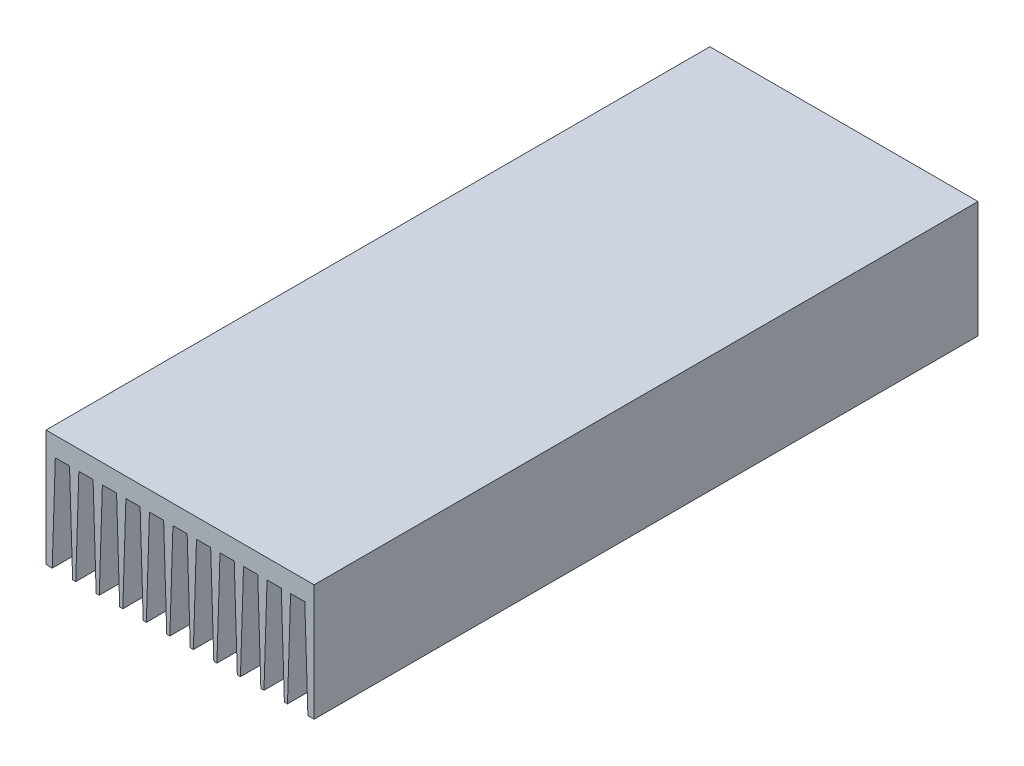
SolidWorks part; units mm, degrees
ref_plane "Plano frontal" through (0, 0, 0) normal (0, 0, 1) x (1, 0, 0)
ref_plane "Plano superior" through (0, 0, 0) normal (0, 1, 0) x (1, 0, 0)
ref_plane "Plano direito" through (0, 0, 0) normal (1, 0, 0) x (0, 0, -1)
sketch "Esboço1" plane through (0, 0, 0) normal (0, 0, 1) x (1, 0, 0)
  line L0 (0.117, 0.0008) -> (0.117, 50.0008)
  line L1 (0.117, 50.0008) -> (115.217, 50.0008)
  line L2 (115.217, 50.0008) -> (115.217, 0.0008)
  line L3 (0.117, 0.0008) -> (115.217, 0.0008) construction
  line L4 (0.117, 41.7008) -> (4.117, 41.7008) construction
  line L5 (4.117, 41.7008) -> (10.217, 41.7008)
  line L6 (10.217, 41.7008) -> (14.217, 41.7008) construction
  line L7 (14.217, 41.7008) -> (20.317, 41.7008)
  line L8 (20.317, 41.7008) -> (24.317, 41.7008) construction
  line L9 (24.317, 41.7008) -> (30.417, 41.7008)
  line L10 (30.417, 41.7008) -> (34.417, 41.7008) construction
  line L11 (34.417, 41.7008) -> (40.517, 41.7008)
  line L12 (40.517, 41.7008) -> (44.517, 41.7008) construction
  line L13 (44.517, 41.7008) -> (50.617, 41.7008)
  line L14 (50.617, 41.7008) -> (54.617, 41.7008) construction
  line L15 (54.617, 41.7008) -> (60.717, 41.7008)
  line L16 (60.717, 41.7008) -> (64.717, 41.7008) construction
  line L17 (64.717, 41.7008) -> (70.817, 41.7008)
  line L18 (70.817, 41.7008) -> (74.817, 41.7008) construction
  line L19 (74.817, 41.7008) -> (80.917, 41.7008)
  line L20 (80.917, 41.7008) -> (84.917, 41.7008) construction
  line L21 (84.917, 41.7008) -> (91.017, 41.7008)
  line L22 (91.017, 41.7008) -> (95.017, 41.7008) construction
  line L23 (95.017, 41.7008) -> (101.117, 41.7008)
  line L24 (101.117, 41.7008) -> (105.117, 41.7008) construction
  line L25 (105.117, 41.7008) -> (111.217, 41.7008)
  line L26 (111.217, 41.7008) -> (115.217, 41.7008) construction
  line L27 (4.117, 41.7008) -> (2.7863, -0.0407)
  line L28 (2.7863, -0.0407) -> (0.117, 0.0008)
  line L29 (10.217, 41.7008) -> (11.5474, 0.0008)
  line L30 (11.5474, 0.0008) -> (12.8876, 0.0008)
  line L31 (12.8876, 0.0008) -> (14.217, 41.7008)
  line L32 (20.317, 41.7008) -> (21.6474, 0.0008)
  line L33 (21.6474, 0.0008) -> (22.9876, 0.0008)
  line L34 (22.9876, 0.0008) -> (24.317, 41.7008)
  line L35 (30.417, 41.7008) -> (31.7474, 0.0008)
  line L36 (31.7474, 0.0008) -> (33.0876, 0.0008)
  line L37 (33.0876, 0.0008) -> (34.417, 41.7008)
  line L38 (44.517, 41.7008) -> (43.1876, 0.0008)
  line L39 (43.1876, 0.0008) -> (41.8474, 0.0008)
  line L40 (41.8474, 0.0008) -> (40.517, 41.7008)
  line L41 (54.617, 41.7008) -> (53.2876, 0.0008)
  line L42 (53.2876, 0.0008) -> (51.9474, 0.0008)
  line L43 (51.9474, 0.0008) -> (50.617, 41.7008)
  line L44 (64.717, 41.7008) -> (63.3876, 0.0008)
  line L45 (63.3876, 0.0008) -> (62.0474, 0.0008)
  line L46 (62.0474, 0.0008) -> (60.717, 41.7008)
  line L47 (74.817, 41.7008) -> (73.4876, 0.0008)
  line L48 (73.4876, 0.0008) -> (72.1474, 0.0008)
  line L49 (72.1474, 0.0008) -> (70.817, 41.7008)
  line L50 (84.917, 41.7008) -> (83.5876, 0.0008)
  line L51 (83.5876, 0.0008) -> (82.2474, 0.0008)
  line L52 (82.2474, 0.0008) -> (80.917, 41.7008)
  line L53 (95.017, 41.7008) -> (93.6876, 0.0008)
  line L54 (93.6876, 0.0008) -> (92.3474, 0.0008)
  line L55 (92.3474, 0.0008) -> (91.017, 41.7008)
  line L56 (101.117, 41.7008) -> (102.4474, 0.0008)
  line L57 (102.4474, 0.0008) -> (103.7876, 0.0008)
  line L58 (103.7876, 0.0008) -> (105.117, 41.7008)
  line L59 (111.217, 41.7008) -> (112.5474, 0.0008)
  line L60 (112.5474, 0.0008) -> (115.217, 0.0008)
  point P26 (0, 0)
  point P43 (0, 0)
  point P47 (0, 0)
  dimension "D1" = 50
  dimension "D2" = 115.1
  dimension "D3" = 6.1
  dimension "D4" = 4
  dimension "D5" = 8.3
extrude "Ressalto-extrusão1" add sketch "Esboço1" along normal blind 285
